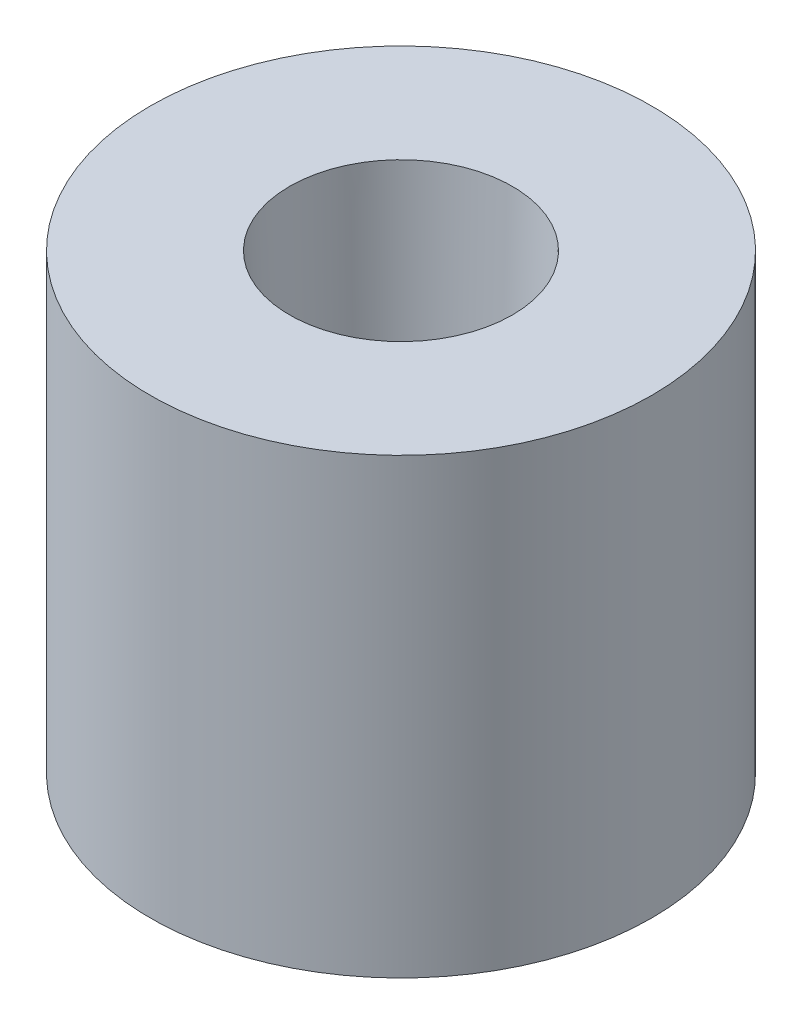
SolidWorks part; units mm, degrees
ref_plane "Front Plane" through (0, 0, 0) normal (0, 0, 1) x (1, 0, 0)
ref_plane "Top Plane" through (0, 0, 0) normal (0, 1, 0) x (1, 0, 0)
ref_plane "Right Plane" through (0, 0, 0) normal (1, 0, 0) x (0, 0, -1)
sketch "Sketch1" plane through (0, 0, 0) normal (0, 0, 1) x (1, 0, 0)
  line L0 (0, 0) -> (-3.6, 0)
  line L3 (-3.6, 0) -> (-3.6, 6.5)
  line L4 (-3.6, 6.5) -> (-1.6, 6.5)
  line L5 (-1.6, 6.5) -> (-1.43, 1.5)
  line L6 (-1.43, 1.5) -> (0, 1.5)
  line L7 (0, 1.5) -> (0, 0)
  dimension "D1" = 1.43
  dimension "D2" = 1.6
  dimension "D3" = 1.5
  dimension "D4" = 2
  dimension "D5" = 5
revolve "Revolve1" add sketch "Sketch1" angle 360 about L7
